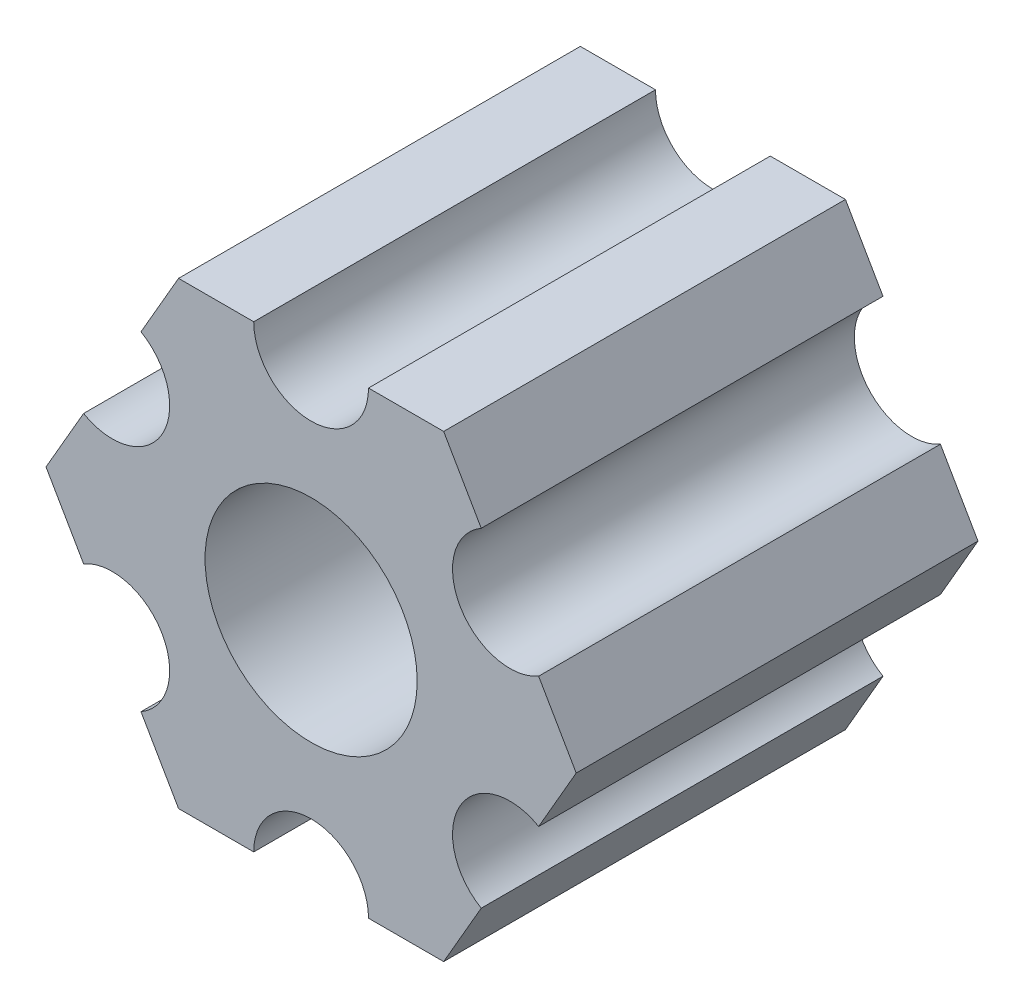
SolidWorks part; units mm, degrees
ref_plane "Front Plane" through (0, 0, 0) normal (0, 0, 1) x (1, 0, 0)
ref_plane "Top Plane" through (0, 0, 0) normal (0, 1, 0) x (1, 0, 0)
ref_plane "Right Plane" through (0, 0, 0) normal (1, 0, 0) x (0, 0, -1)
ref_plane "Plane1" through (0, 0, 0) normal (0, 0, -1) x (-1, 0, 0)
sketch "Sketch1" plane through (0, 0, 0) normal (0, 0, -1) x (-1, 0, 0)
  line L0 (-4.7055, -4.5498) -> (-3.6662, -6.35)
  line L1 (-3.6662, -6.35) -> (-1.5875, -6.35)
  line L2 (1.5875, -6.35) -> (3.6662, -6.35)
  line L3 (3.6662, -6.35) -> (4.7055, -4.5498)
  line L4 (6.293, -1.8002) -> (7.3323, 0)
  line L5 (7.3323, 0) -> (6.293, 1.8002)
  line L6 (4.7055, 4.5498) -> (3.6662, 6.35)
  line L7 (3.6662, 6.35) -> (1.5875, 6.35)
  line L8 (-1.5875, 6.35) -> (-3.6662, 6.35)
  line L9 (-3.6662, 6.35) -> (-4.7055, 4.5498)
  line L10 (-6.293, 1.8002) -> (-7.3323, 0)
  line L11 (-7.3323, 0) -> (-6.293, -1.8002)
  circle A0 centre (0, 0) radius 2.9337
  arc A1 (-6.293, -1.8002) -> (-4.7055, -4.5498) centre (-5.4993, -3.175) cw
  arc A2 (-1.5875, -6.35) -> (1.5875, -6.35) centre (0, -6.35) cw
  arc A3 (4.7055, -4.5498) -> (6.293, -1.8002) centre (5.4993, -3.175) cw
  arc A4 (6.293, 1.8002) -> (4.7055, 4.5498) centre (5.4993, 3.175) cw
  arc A5 (1.5875, 6.35) -> (-1.5875, 6.35) centre (0, 6.35) cw
  arc A6 (-4.7055, 4.5498) -> (-6.293, 1.8002) centre (-5.4993, 3.175) cw
extrude "Boss-Extrude1" add sketch "Sketch1" against normal blind 15.875
sketch "Sketch3" plane through (0, 0, 15.875) normal (0, 0, 1) x (1, 0, 0)
  line L0 (-4.7055, 4.5498) -> (-3.6662, 6.35) construction
  line L1 (-3.6662, 6.35) -> (-1.5875, 6.35) construction
  line L2 (1.5875, 6.35) -> (3.6662, 6.35) construction
  line L3 (3.6662, 6.35) -> (4.7055, 4.5498) construction
  line L4 (6.293, 1.8002) -> (7.3323, 0) construction
  line L5 (7.3323, 0) -> (6.293, -1.8002) construction
  line L6 (4.7055, -4.5498) -> (3.6662, -6.35) construction
  line L7 (3.6662, -6.35) -> (1.5875, -6.35) construction
  line L8 (-1.5875, -6.35) -> (-3.6662, -6.35) construction
  line L9 (-3.6662, -6.35) -> (-4.7055, -4.5498) construction
  line L10 (-6.293, -1.8002) -> (-7.3323, 0) construction
  line L11 (-7.3323, 0) -> (-6.293, 1.8002) construction
  line L12 (-4.7055, 4.5498) -> (-3.6662, 6.35)
  line L13 (-3.6662, 6.35) -> (-1.5875, 6.35)
  line L14 (1.5875, 6.35) -> (3.6662, 6.35)
  line L15 (3.6662, 6.35) -> (4.7055, 4.5498)
  line L16 (6.293, 1.8002) -> (7.3323, 0)
  line L17 (7.3323, 0) -> (6.293, -1.8002)
  line L18 (4.7055, -4.5498) -> (3.6662, -6.35)
  line L19 (3.6662, -6.35) -> (1.5875, -6.35)
  line L20 (-1.5875, -6.35) -> (-3.6662, -6.35)
  line L21 (-3.6662, -6.35) -> (-4.7055, -4.5498)
  line L22 (-6.293, -1.8002) -> (-7.3323, 0)
  line L23 (-7.3323, 0) -> (-6.293, 1.8002)
  arc A0 (-1.5875, 6.35) -> (1.5875, 6.35) centre (0, 6.35) ccw construction
  arc A1 (4.7055, 4.5498) -> (6.293, 1.8002) centre (5.4993, 3.175) ccw construction
  arc A2 (6.293, -1.8002) -> (4.7055, -4.5498) centre (5.4993, -3.175) ccw construction
  arc A3 (1.5875, -6.35) -> (-1.5875, -6.35) centre (0, -6.35) ccw construction
  arc A4 (-4.7055, -4.5498) -> (-6.293, -1.8002) centre (-5.4993, -3.175) ccw construction
  arc A5 (-6.293, 1.8002) -> (-4.7055, 4.5498) centre (-5.4993, 3.175) ccw construction
  arc A6 (-1.5875, 6.35) -> (1.5875, 6.35) centre (0, 6.35) ccw
  arc A7 (4.7055, 4.5498) -> (6.293, 1.8002) centre (5.4993, 3.175) ccw
  arc A8 (6.293, -1.8002) -> (4.7055, -4.5498) centre (5.4993, -3.175) ccw
  arc A9 (1.5875, -6.35) -> (-1.5875, -6.35) centre (0, -6.35) ccw
  arc A10 (-4.7055, -4.5498) -> (-6.293, -1.8002) centre (-5.4993, -3.175) ccw
  arc A11 (-6.293, 1.8002) -> (-4.7055, 4.5498) centre (-5.4993, 3.175) ccw
extrude "Cut-Extrude1" cut sketch "Sketch3" against normal blind 4.7625
